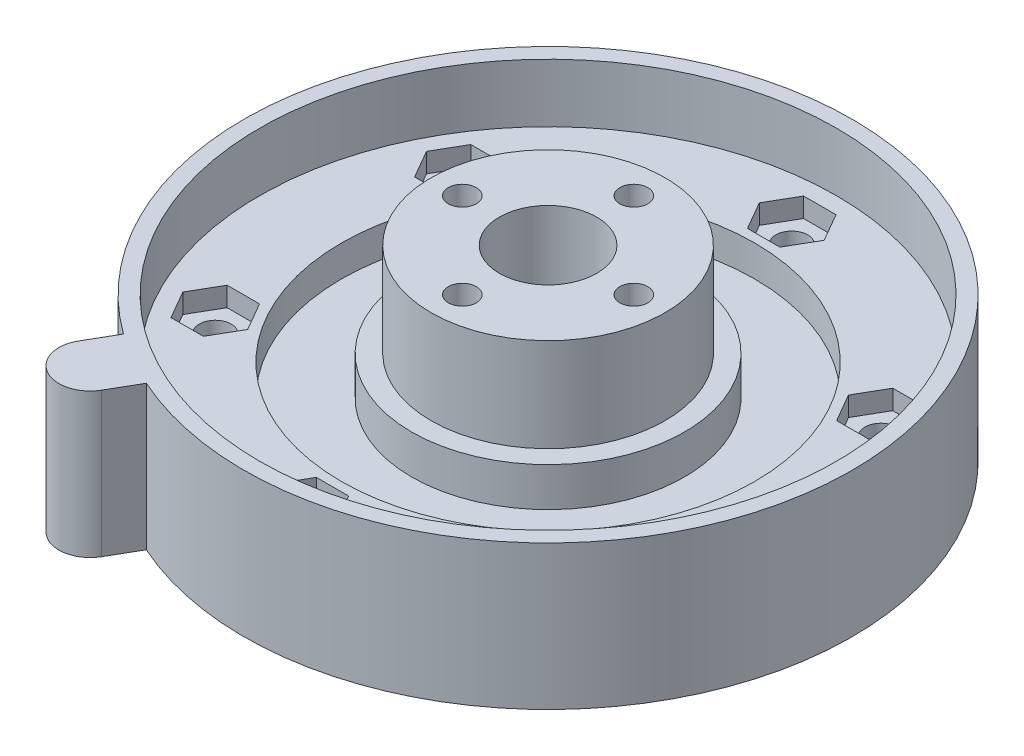
SolidWorks part; units mm, degrees
ref_plane "Front Plane" through (0, 0, 0) normal (0, 0, 1) x (1, 0, 0)
ref_plane "Top Plane" through (0, 0, 0) normal (0, 1, 0) x (1, 0, 0)
ref_plane "Right Plane" through (0, 0, 0) normal (1, 0, 0) x (0, 0, -1)
sketch "Sketch1" plane through (0, 0, 0) normal (0, 1, 0) x (1, 0, 0)
  circle A0 centre (0, 0) radius 39
  dimension "D1" = 78
extrude "Boss-Extrude1" add sketch "Sketch1" along normal blind 18.5
sketch "Sketch2" plane through (0, 18.5, 0) normal (0, 1, 0) x (1, 0, 0)
  circle A2 centre (0, 0) radius 37
  circle A3 centre (0, 0) radius 37
  dimension "D1" = 2
extrude "Cut-Extrude1" cut sketch "Sketch2" against normal blind 7.5
sketch "Sketch3" plane through (0, 11, 0) normal (0, 1, 0) x (1, 0, 0)
  circle A0 centre (0, 0) radius 26.5
  dimension "D1" = 53
extrude "Cut-Extrude2" cut sketch "Sketch3" against normal blind 4
sketch "Sketch4" plane through (0, 7, 0) normal (0, 1, 0) x (1, 0, 0)
  circle A0 centre (0, 0) radius 17.5
  dimension "D1" = 35
extrude "Boss-Extrude2" add sketch "Sketch4" along normal blind 5
sketch "Sketch5" plane through (0, 12, 0) normal (0, 1, 0) x (1, 0, 0)
  circle A0 centre (0, 0) radius 15
  dimension "D1" = 30
extrude "Boss-Extrude3" add sketch "Sketch5" along normal blind 12
sketch "Sketch6" plane through (0, 24, 0) normal (0, 1, 0) x (1, 0, 0)
  circle A0 centre (0, 0) radius 6.25
  circle A1 centre (0, 11) radius 1.8
  circle A2 centre (11, 0) radius 1.8
  circle A3 centre (0, -11) radius 1.8
  circle A4 centre (-11, 0) radius 1.8
  dimension "D1" = 12.5
  dimension "D2" = 3.6
  dimension "D3" = 11
  dimension "D4" = 4
extrude "Cut-Extrude3" cut sketch "Sketch6" against normal through all
hole_wizard "CSK for M4 Countersunk Flat Head Screw1" positions "3DSketch1" profile "Sketch8" countersink size "M4" standard "ISO" end condition through all
sketch3d "3DSketch1"
  line L0 (0, 0, 11) -> (0, 24, 11) construction
  line L1 (11, 0, 0) -> (11, 24, 0) construction
  line L2 (0, 0, -11) -> (0, 24, -11) construction
  line L3 (-11, 0, 0) -> (-11, 24, 0) construction
  point P0 (0, 0, 11)
  point P4 (11, 0, 0)
  point P8 (0, 0, -11)
  point P12 (-11, 0, 0)
sketch "Sketch8" plane through (0, 0, 11) normal (1, 0, 0) x (0, 0, -1)
  line L0 (0, 0) -> (0, 24)
  line L1 (0, 24) -> (1.75, 24)
  line L2 (1.75, 24) -> (1.75, 2.8)
  line L3 (1.75, 2.8) -> (4.55, 0)
  line L5 (4.55, 0) -> (0, 0)
  line L6 (-1.75, 2.8) -> (-4.55, 0) construction
  line L11 (0, -6.35) -> (0, 107.95) construction
  dimension "Thru Hole Dia." = 3.5
  dimension "Thru Hole Depth" = 24
  dimension "Near C'Sink Dia." = 9.1
  dimension "Near C'Sink Angle" = 90
sketch "Sketch9" plane through (0, 11, 0) normal (0, 1, 0) x (1, 0, 0)
  circle A0 centre (0, 31.25) radius 2.05
  circle A1 centre (27.0633, 15.625) radius 2.05
  circle A2 centre (27.0633, -15.625) radius 2.05
  circle A3 centre (0, -31.25) radius 2.05
  circle A4 centre (-27.0633, -15.625) radius 2.05
  circle A5 centre (-27.0633, 15.625) radius 2.05
  dimension "D2" = 4.1
  dimension "D1" = 31.25
  dimension "D3" = 6
extrude "Cut-Extrude4" cut sketch "Sketch9" against normal through all
sketch "Sketch10" plane through (0, 11, 0) normal (0, 1, 0) x (1, 0, 0)
  line L1 (2.0785, 34.85) -> (-2.0785, 34.85)
  line L2 (-2.0785, 34.85) -> (-4.1569, 31.25)
  line L3 (-4.1569, 31.25) -> (-2.0785, 27.65)
  line L4 (-2.0785, 27.65) -> (2.0785, 27.65)
  line L5 (2.0785, 27.65) -> (4.1569, 31.25)
  line L6 (4.1569, 31.25) -> (2.0785, 34.85)
  circle A0 centre (0, 31.25) radius 3.6 construction
  dimension "D1" = 7.2
extrude "Cut-Extrude5" cut sketch "Sketch10" against normal blind 2.5
pattern_circular "CirPattern1" count 6 over 360 about axis through (0, 0, 0) along (0, 1, 0) of "Cut-Extrude5"
sketch "Sketch11" plane through (0, 18.5, 0) normal (0, 1, 0) x (1, 0, 0)
  line L0 (-21.5, -37.2391) -> (0, 0) construction
  line L1 (0, 0) -> (0, -39) construction
  line L2 (-18.0359, -39.2391) -> (-15.9331, -35.5969)
  line L3 (-24.9641, -35.2391) -> (-22.8613, -31.5969)
  line L4 (0, -8) -> (3.4641, -2)
  line L5 (-18.0359, -39.2391) -> (3.4641, -2) construction
  line L6 (-24.9641, -35.2391) -> (-3.4641, 2) construction
  circle A0 centre (-21.5, -37.2391) radius 4
  circle A1 centre (0, 0) radius 39 construction
  circle A2 centre (0, 0) radius 39
  circle M5 centre (0, 0) radius 39
  dimension "D3" = 8
  dimension "D1" = 30
  dimension "D2" = 43
  dimension "D4" = 4
  dimension "D5" = 4
extrude "Boss-Extrude5" add sketch "Sketch11" against normal through all contours A0 | A0 L2 M5 | A0 L3 M5
